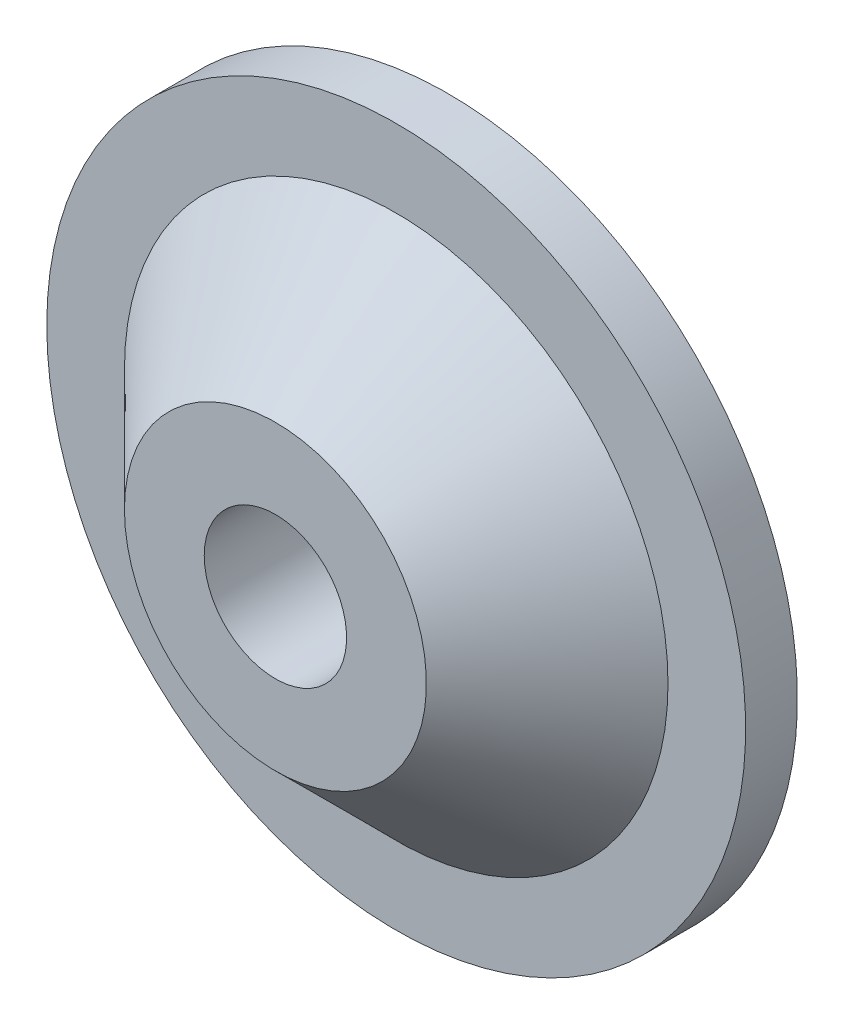
SolidWorks part; units mm, degrees
ref_plane "Front Plane" through (0, 0, 0) normal (0, 0, 1) x (1, 0, 0)
ref_plane "Top Plane" through (0, 0, 0) normal (0, 1, 0) x (1, 0, 0)
ref_plane "Right Plane" through (0, 0, 0) normal (1, 0, 0) x (0, 0, -1)
sketch "Sketch3" plane through (0, 0, 0) normal (0, 1, 0) x (1, 0, 0)
  line L0 (0, 35.5801) -> (0, 0)
  line L1 (6.3, 0) -> (8.1, 0)
  line L2 (8.1, 0) -> (8.1, 1.2)
  line L3 (8.1, 1.2) -> (1.65, 1.2)
  line L4 (1.65, 1.2) -> (1.65, 0)
  line L5 (3.5, -2.8) -> (-3.5, -2.8) construction
  line L6 (3.5, -2.8) -> (-3.5, -2.8) construction
  line L7 (1.65, 0) -> (1.65, -2.8)
  line L8 (1.65, -2.8) -> (3.5, -2.8)
  line L9 (3.5, -2.8) -> (6.3, 0)
  dimension "D1" = 8.1
  dimension "D2" = 1.65
  dimension "D3" = 1.2
revolve "Revolve1" add sketch "Sketch3" angle 360 about L0
chamfer "Chamfer1" distance 0.5 angle 45 1 edges at (-1.65, 0, -1.2)
equation "\"`6.4\"=107.223"
